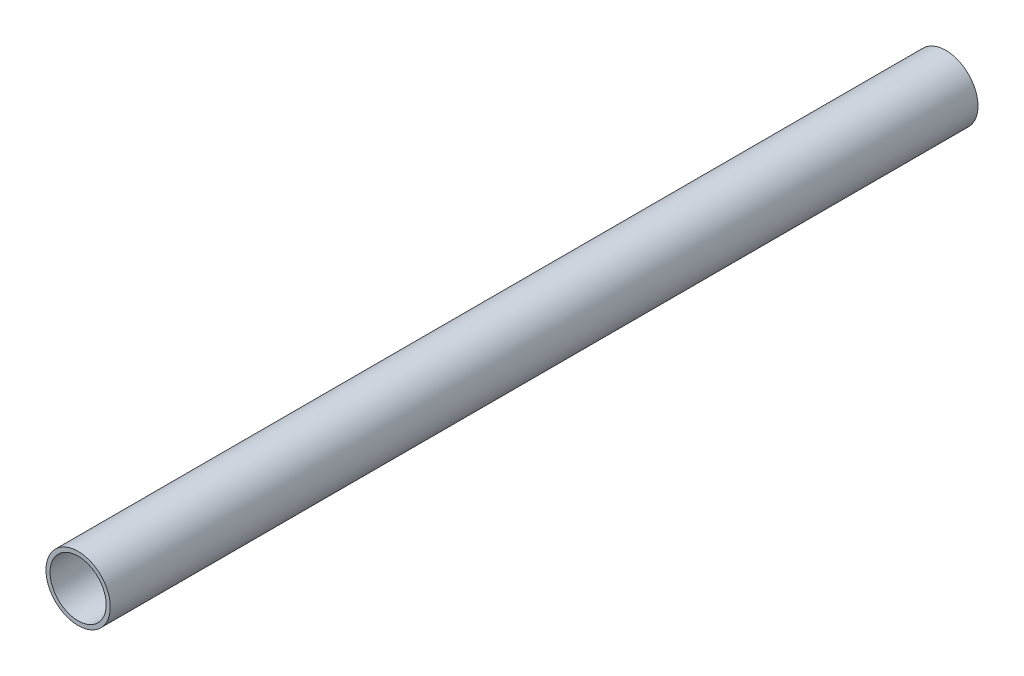
SolidWorks part; units mm, degrees
material "PVC Rigid"
ref_plane "Front Plane" through (0, 0, 0) normal (0, 0, 1) x (1, 0, 0)
ref_plane "Top Plane" through (0, 0, 0) normal (0, 1, 0) x (1, 0, 0)
ref_plane "Right Plane" through (0, 0, 0) normal (1, 0, 0) x (0, 0, -1)
sketch "Sketch1" plane through (0, 0, 0) normal (0, 0, 1) x (1, 0, 0)
  circle A0 centre (0, 0) radius 18.923
  circle A1 centre (0, 0) radius 16.51
  dimension "D1" = 37.846
  dimension "D2" = 33.02
extrude "Boss-Extrude1" add sketch "Sketch1" along normal blind 510.54
